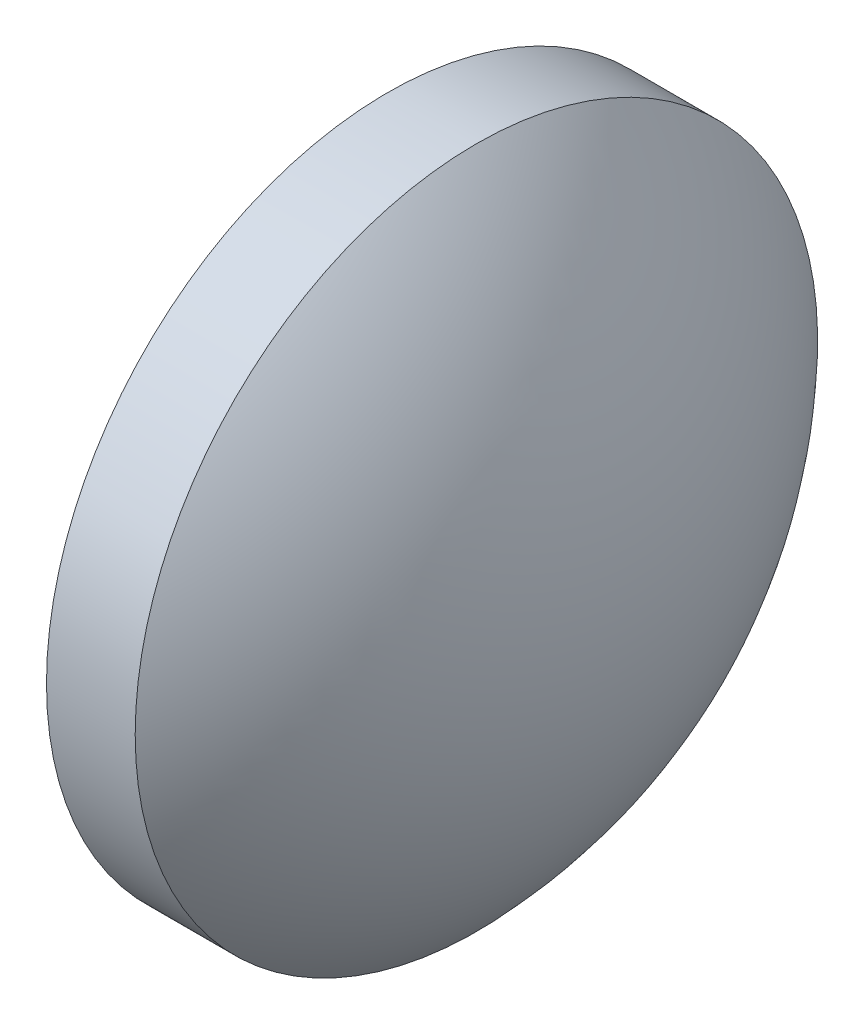
SolidWorks part; units mm, degrees
ref_plane "前视基准面" through (0, 0, 0) normal (0, 0, 1) x (1, 0, 0)
ref_plane "上视基准面" through (0, 0, 0) normal (0, 1, 0) x (1, 0, 0)
ref_plane "右视基准面" through (0, 0, 0) normal (1, 0, 0) x (0, 0, -1)
sketch "草图1" plane through (0, 0, 0) normal (0, 0, 1) x (1, 0, 0)
  line L0 (407.4544, 122.1833) -> (413.106, 122.1833) construction
  line L1 (408.5966, 122.1833) -> (408.5966, 127.1833)
  line L2 (411.8966, 122.1833) -> (408.5966, 122.1833)
  line L5 (408.5966, 127.1833) -> (409.8966, 127.1833)
  arc A0 (411.8966, 122.1833) -> (409.8966, 127.1833) centre (404.6466, 122.1833) ccw
revolve "旋转1" add sketch "草图1" angle 360 about L0
